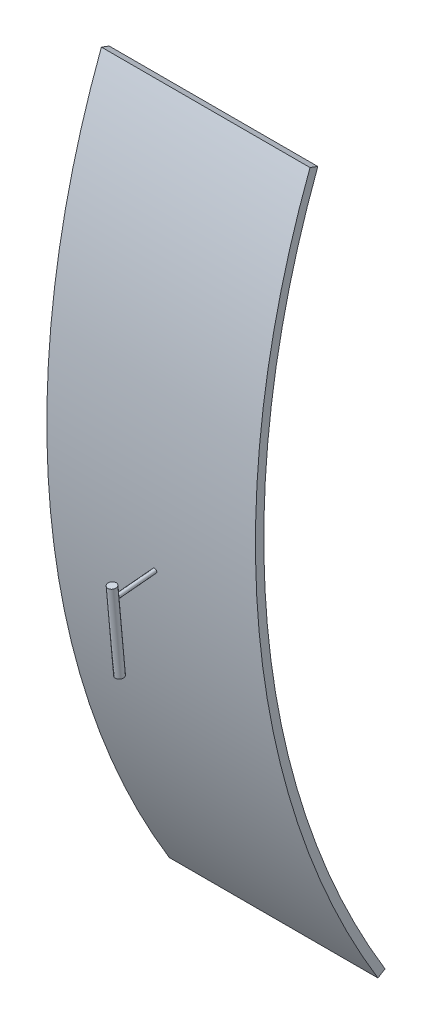
SolidWorks part; units mm, degrees
ref_plane "Front Plane" through (0, 0, 0) normal (0, 0, 1) x (1, 0, 0)
ref_plane "Top Plane" through (0, 0, 0) normal (0, 1, 0) x (1, 0, 0)
ref_plane "Right Plane" through (0, 0, 0) normal (1, 0, 0) x (0, 0, -1)
sketch "Sketch1" plane through (0, 0, 0) normal (1, 0, 0) x (0, 0, -1)
  line L2 (-188.9259, 71.4913) -> (-187.0554, 70.7834)
  line L3 (-172.6503, -104.8612) -> (-170.9409, -103.823)
  line L4 (-170.9409, -103.823) -> (-170.4328, -104.3773)
  arc A0 (-187.0554, 70.7834) -> (-170.9409, -103.823) centre (0, 0) ccw
  arc A1 (-172.6503, -104.8612) -> (-188.9259, 71.4913) centre (0, 0) cw
  point P6 (-201.1452, -18.5637)
extrude "Boss-Extrude1" add sketch "Sketch1" along normal blind 50 contours L3 A1 L2 A0
ref_plane "Plane1" through (0, -18.5637, 201.1452) normal (0, -0.0919, 0.9958) x (1, 0, 0)
sketch "Sketch2" plane through (0, -18.5637, 201.1452) normal (0, -0.0919, 0.9958) x (1, 0, 0)
  circle A0 centre (25, 0) radius 0.5
  point P11 (25, 0)
extrude "Boss-Extrude2" add sketch "Sketch2" along normal blind 10 separate body contours A0
ref_plane "Plane2" through (0, -19.4827, 211.1029) normal (0, -0.0919, 0.9958) x (1, 0, 0)
sketch "Sketch3" plane through (0, -19.4827, 211.1029) normal (0, -0.0919, 0.9958) x (1, 0, 0)
  line L1 (25, 2.9531) -> (26, 2.9531)
  line L2 (25, 2.9531) -> (25, -16.7066)
  line L3 (25, -16.7066) -> (26, -16.7066)
  line L4 (26, 2.9531) -> (26, -16.7066)
  point P0 (25, 0)
revolve "Revolve1" add sketch "Sketch3" angle 360 about L2
